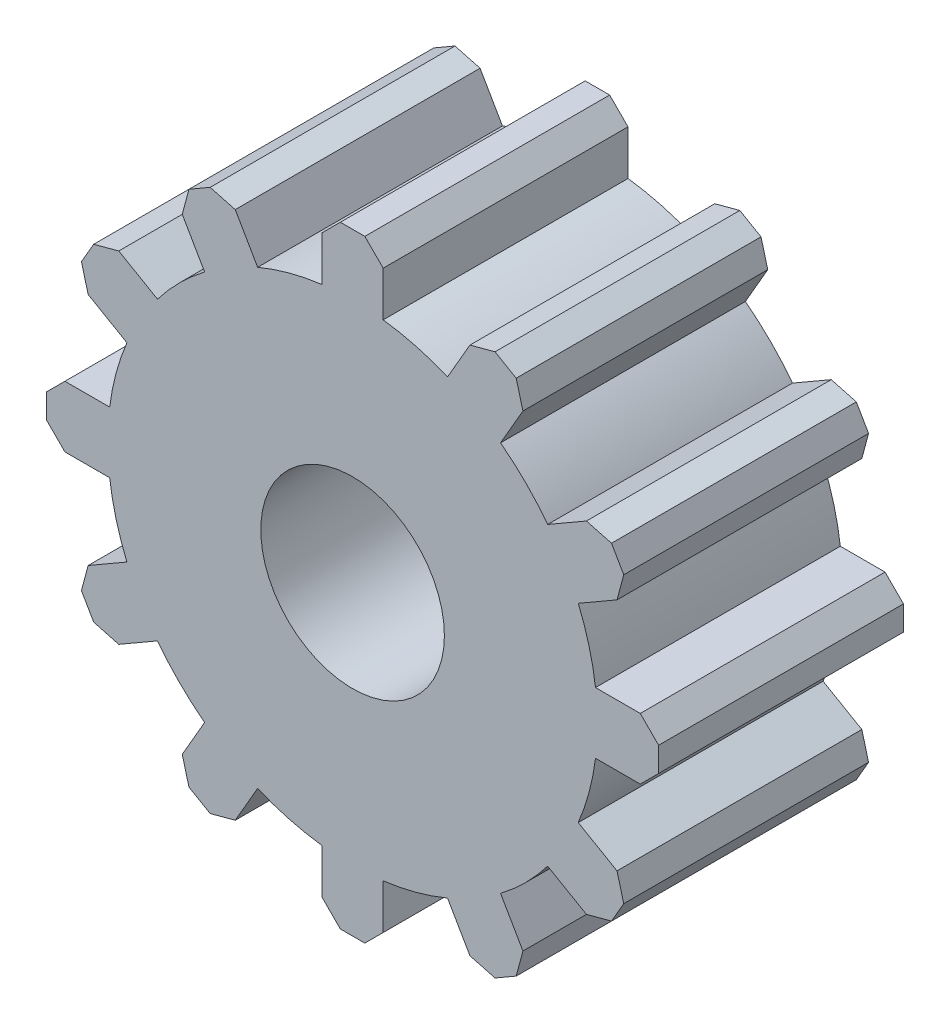
SolidWorks part; units mm, degrees
ref_plane "Front Plane" through (0, 0, 0) normal (0, 0, 1) x (1, 0, 0)
ref_plane "Top Plane" through (0, 0, 0) normal (0, 1, 0) x (1, 0, 0)
ref_plane "Right Plane" through (0, 0, 0) normal (1, 0, 0) x (0, 0, -1)
sketch "Sketch1" plane through (0, 0, 0) normal (0, 0, 1) x (1, 0, 0)
  circle A0 centre (0, 0) radius 101.6
extrude "Boss-Extrude1" add sketch "Sketch1" along normal mid plane 101.6
sketch "Sketch2" plane through (0, 0, 50.8) normal (0, 0, 1) x (1, 0, 0)
  line L0 (74.4985, 103.6352) -> (52.5015, 116.3352)
  line L1 (39.403, 93.6481) -> (52.5015, 116.3352)
  line L2 (12.7, 100.8031) -> (12.7, 127)
  line L3 (12.7, 127) -> (-12.7, 127)
  line L4 (-12.7, 100.8031) -> (-12.7, 127)
  line L5 (0, 101.6) -> (-12.7, 127) construction
  line L6 (12.7, 127) -> (0, 101.6) construction
  line L7 (61.4001, 80.9481) -> (74.4985, 103.6352)
  line L8 (116.3352, 52.5015) -> (103.6352, 74.4985)
  line L9 (80.9481, 61.4001) -> (103.6352, 74.4985)
  line L10 (93.6481, 39.403) -> (116.3352, 52.5015)
  line L11 (127, -12.7) -> (127, 12.7)
  line L12 (100.8031, 12.7) -> (127, 12.7)
  line L13 (100.8031, -12.7) -> (127, -12.7)
  line L14 (103.6352, -74.4985) -> (116.3352, -52.5015)
  line L15 (93.6481, -39.403) -> (116.3352, -52.5015)
  line L16 (80.9481, -61.4001) -> (103.6352, -74.4985)
  line L17 (52.5015, -116.3352) -> (74.4985, -103.6352)
  line L18 (61.4001, -80.9481) -> (74.4985, -103.6352)
  line L19 (39.403, -93.6481) -> (52.5015, -116.3352)
  line L20 (-12.7, -127) -> (12.7, -127)
  line L21 (12.7, -100.8031) -> (12.7, -127)
  line L22 (-12.7, -100.8031) -> (-12.7, -127)
  line L23 (-74.4985, -103.6352) -> (-52.5015, -116.3352)
  line L24 (-39.403, -93.6481) -> (-52.5015, -116.3352)
  line L25 (-61.4001, -80.9481) -> (-74.4985, -103.6352)
  line L26 (-116.3352, -52.5015) -> (-103.6352, -74.4985)
  line L27 (-80.9481, -61.4001) -> (-103.6352, -74.4985)
  line L28 (-93.6481, -39.403) -> (-116.3352, -52.5015)
  line L29 (-127, 12.7) -> (-127, -12.7)
  line L30 (-100.8031, -12.7) -> (-127, -12.7)
  line L31 (-100.8031, 12.7) -> (-127, 12.7)
  line L32 (-103.6352, 74.4985) -> (-116.3352, 52.5015)
  line L33 (-93.6481, 39.403) -> (-116.3352, 52.5015)
  line L34 (-80.9481, 61.4001) -> (-103.6352, 74.4985)
  line L35 (-52.5015, 116.3352) -> (-74.4985, 103.6352)
  line L36 (-61.4001, 80.9481) -> (-74.4985, 103.6352)
  line L37 (-39.403, 93.6481) -> (-52.5015, 116.3352)
  circle A0 centre (0, 0) radius 101.6 construction
  arc A1 (-39.403, 93.6481) -> (-61.4001, 80.9481) centre (0, 0) ccw
  arc A2 (-80.9481, 61.4001) -> (-93.6481, 39.403) centre (0, 0) ccw
  arc A3 (-100.8031, 12.7) -> (-100.8031, -12.7) centre (0, 0) ccw
  arc A4 (-93.6481, -39.403) -> (-80.9481, -61.4001) centre (0, 0) ccw
  arc A5 (-61.4001, -80.9481) -> (-39.403, -93.6481) centre (0, 0) ccw
  arc A6 (-12.7, -100.8031) -> (12.7, -100.8031) centre (0, 0) ccw
  arc A7 (39.403, -93.6481) -> (61.4001, -80.9481) centre (0, 0) ccw
  arc A8 (80.9481, -61.4001) -> (93.6481, -39.403) centre (0, 0) ccw
  arc A9 (100.8031, -12.7) -> (100.8031, 12.7) centre (0, 0) ccw
  arc A10 (93.6481, 39.403) -> (80.9481, 61.4001) centre (0, 0) ccw
  arc A11 (61.4001, 80.9481) -> (39.403, 93.6481) centre (0, 0) ccw
  arc A12 (12.7, 100.8031) -> (-12.7, 100.8031) centre (0, 0) ccw
  point P0 (0, 101.6)
  point P55 (0, 0)
  dimension "D1" = 25.4
  dimension "D2" = 25.4
  dimension "D3" = 12
extrude "Boss-Extrude2" add sketch "Sketch2" against normal through all
chamfer "Chamfer1" distance 7.62 angle 45 24 edges at (-103.6352, -74.4985, 0) (-52.5015, -116.3352, 0) (12.7, -127, 0) (52.5015, -116.3352, 0) (74.4985, -103.6352, 0) (103.6352, -74.4985, 0) (127, -12.7, 0) (116.3352, 52.5015, 0) (74.4985, 103.6352, 0) (12.7, 127, 0) (-74.4985, 103.6352, 0) (-116.3352, 52.5015, 0) (-103.6352, 74.4985, 0) (-127, -12.7, 0) (-127, 12.7, 0) (-116.3352, -52.5015, 0) (-74.4985, -103.6352, 0) (-12.7, -127, 0) (116.3352, -52.5015, 0) (127, 12.7, 0) (103.6352, 74.4985, 0) (52.5015, 116.3352, 0) (-52.5015, 116.3352, 0) (-12.7, 127, 0)
sketch "Sketch3" plane through (0, 0, 50.8) normal (0, 0, 1) x (1, 0, 0)
  circle A0 centre (0, 0) radius 38.1
extrude "Cut-Extrude1" cut sketch "Sketch3" against normal through all
